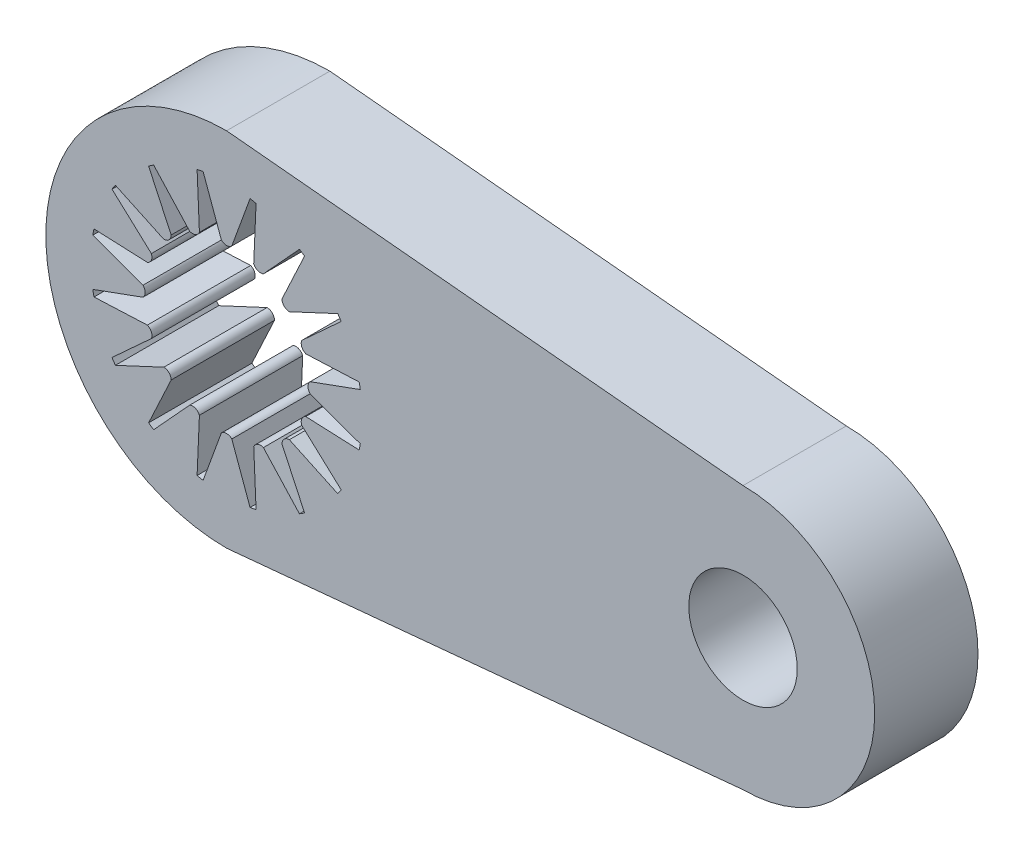
SolidWorks part; units mm, degrees
ref_plane "Ebene vorne" through (0, 0, 0) normal (0, 0, 1) x (1, 0, 0)
ref_plane "Ebene oben" through (0, 0, 0) normal (0, 1, 0) x (1, 0, 0)
ref_plane "Ebene rechts" through (0, 0, 0) normal (1, 0, 0) x (0, 0, -1)
sketch "Sketch1" plane through (0, 0, 0) normal (0, 0, 1) x (1, 0, 0)
  line L32 (12.1788, 4.8622) -> (22.1788, 4.8622) construction
  line L33 (12.1788, 8.3622) -> (22.1788, 7.4122)
  line L34 (12.1788, 1.3622) -> (22.1788, 2.3122)
  line L64 (11.653, 3.3285) -> (11.6192, 2.5524)
  line L65 (11.812, 2.514) -> (12.0777, 3.2441)
  line L66 (12.28, 3.2441) -> (12.5457, 2.514)
  line L67 (12.7385, 2.5524) -> (12.7046, 3.3285)
  line L68 (12.8915, 3.4059) -> (13.4164, 2.8332)
  line L69 (13.5799, 2.9424) -> (13.2515, 3.6465)
  line L70 (13.3946, 3.7895) -> (14.0986, 3.4612)
  line L71 (14.2079, 3.6247) -> (13.6351, 4.1495)
  line L72 (13.7125, 4.3364) -> (14.4886, 4.3025)
  line L73 (14.527, 4.4954) -> (13.797, 4.7611)
  line L74 (13.797, 4.9633) -> (14.527, 5.229)
  line L75 (14.4886, 5.4219) -> (13.7125, 5.388)
  line L76 (13.6351, 5.5749) -> (14.2079, 6.0997)
  line L77 (14.0986, 6.2632) -> (13.3946, 5.9349)
  line L78 (13.2515, 6.0779) -> (13.5799, 6.782)
  line L79 (13.4164, 6.8912) -> (12.8915, 6.3185)
  line L80 (12.7046, 6.3959) -> (12.7385, 7.172)
  line L81 (12.5457, 7.2104) -> (12.28, 6.4803)
  line L82 (12.0777, 6.4803) -> (11.812, 7.2104)
  line L83 (11.6192, 7.172) -> (11.653, 6.3959)
  line L84 (11.4662, 6.3185) -> (10.9413, 6.8912)
  line L85 (10.7778, 6.782) -> (11.1062, 6.0779)
  line L86 (10.9631, 5.9349) -> (10.259, 6.2632)
  line L87 (10.1498, 6.0997) -> (10.7226, 5.5749)
  line L88 (10.6452, 5.388) -> (9.869, 5.4219)
  line L89 (9.8307, 5.229) -> (10.5607, 4.9633)
  line L90 (10.5607, 4.7611) -> (9.8307, 4.4954)
  line L91 (9.869, 4.3025) -> (10.6452, 4.3364)
  line L92 (10.7226, 4.1495) -> (10.1498, 3.6247)
  line L93 (10.259, 3.4612) -> (10.9631, 3.7895)
  line L94 (11.1062, 3.6465) -> (10.7778, 2.9424)
  line L95 (10.9413, 2.8332) -> (11.4662, 3.4059)
  line L96 (10.259, 6.2632) -> (10.0259, 6.3719)
  line L97 (9.9602, 6.2735) -> (10.1498, 6.0997)
  line L98 (9.869, 5.4219) -> (9.6121, 5.4331)
  line L99 (9.589, 5.317) -> (9.8307, 5.229)
  line L100 (9.8307, 4.4954) -> (9.589, 4.4074)
  line L101 (9.6121, 4.2913) -> (9.869, 4.3025)
  line L102 (10.0259, 3.3525) -> (10.259, 3.4612)
  line L103 (10.1498, 3.6247) -> (9.9602, 3.4509)
  line L104 (10.7676, 2.6435) -> (10.9413, 2.8332)
  line L105 (10.7778, 2.9424) -> (10.6691, 2.7093)
  line L106 (11.6192, 2.5524) -> (11.6079, 2.2954)
  line L107 (11.724, 2.2724) -> (11.812, 2.514)
  line L108 (12.5457, 2.514) -> (12.6337, 2.2724)
  line L109 (12.7497, 2.2954) -> (12.7385, 2.5524)
  line L110 (13.6885, 2.7093) -> (13.5799, 2.9424)
  line L111 (13.4164, 2.8332) -> (13.5901, 2.6435)
  line L112 (14.0986, 3.4612) -> (14.3317, 3.3525)
  line L113 (14.3975, 3.4509) -> (14.2079, 3.6247)
  line L114 (14.4886, 4.3025) -> (14.7456, 4.2913)
  line L115 (14.7687, 4.4074) -> (14.527, 4.4954)
  line L116 (14.527, 5.229) -> (14.7687, 5.317)
  line L117 (14.7456, 5.4331) -> (14.4886, 5.4219)
  line L118 (14.3317, 6.3719) -> (14.0986, 6.2632)
  line L119 (14.2079, 6.0997) -> (14.3975, 6.2735)
  line L120 (13.5799, 6.782) -> (13.6885, 7.0151)
  line L121 (13.5901, 7.0809) -> (13.4164, 6.8912)
  line L122 (12.7385, 7.172) -> (12.7497, 7.429)
  line L123 (12.6337, 7.452) -> (12.5457, 7.2104)
  line L124 (11.6079, 7.429) -> (11.6192, 7.172)
  line L125 (11.812, 7.2104) -> (11.724, 7.452)
  line L126 (10.6691, 7.0151) -> (10.7778, 6.782)
  line L127 (10.9413, 6.8912) -> (10.7676, 7.0809)
  arc A2 (12.8379, 8.2996) -> (12.8379, 1.4248) centre (12.1788, 4.8622) ccw
  circle A4 centre (22.1788, 4.8622) radius 1.05
  arc A6 (22.1788, 2.3122) -> (22.1788, 7.4122) centre (22.1788, 4.8622) ccw
  arc A64 (11.653, 3.3285) -> (11.4662, 3.4059) centre (11.5209, 3.2738) ccw
  arc A66 (12.28, 3.2441) -> (12.0777, 3.2441) centre (12.1788, 3.1429) ccw
  arc A68 (12.8915, 3.4059) -> (12.7046, 3.3285) centre (12.8368, 3.2738) ccw
  arc A70 (13.3946, 3.7895) -> (13.2515, 3.6465) centre (13.3946, 3.6465) ccw
  arc A72 (13.7125, 4.3364) -> (13.6351, 4.1495) centre (13.7672, 4.2043) ccw
  arc A74 (13.797, 4.9633) -> (13.797, 4.7611) centre (13.8981, 4.8622) ccw
  arc A76 (13.6351, 5.5749) -> (13.7125, 5.388) centre (13.7672, 5.5201) ccw
  arc A78 (13.2515, 6.0779) -> (13.3946, 5.9349) centre (13.3946, 6.0779) ccw
  arc A80 (12.7046, 6.3959) -> (12.8915, 6.3185) centre (12.8368, 6.4506) ccw
  arc A82 (12.0777, 6.4803) -> (12.28, 6.4803) centre (12.1788, 6.5815) ccw
  arc A84 (11.4662, 6.3185) -> (11.653, 6.3959) centre (11.5209, 6.4506) ccw
  arc A86 (10.9631, 5.9349) -> (11.1062, 6.0779) centre (10.9631, 6.0779) ccw
  arc A88 (10.6452, 5.388) -> (10.7226, 5.5749) centre (10.5904, 5.5201) ccw
  arc A90 (10.5607, 4.7611) -> (10.5607, 4.9633) centre (10.4596, 4.8622) ccw
  arc A92 (10.7226, 4.1495) -> (10.6452, 4.3364) centre (10.5904, 4.2043) ccw
  arc A94 (11.1062, 3.6465) -> (10.9631, 3.7895) centre (10.9631, 3.6465) ccw
  arc A97 (10.0259, 6.3719) -> (9.9602, 6.2735) centre (12.1788, 4.8622) ccw
  arc A99 (9.6121, 5.4331) -> (9.589, 5.317) centre (12.1788, 4.8622) ccw
  arc A101 (9.589, 4.4074) -> (9.6121, 4.2913) centre (12.1788, 4.8622) ccw
  arc A103 (9.9602, 3.4509) -> (10.0259, 3.3525) centre (12.1788, 4.8622) ccw
  arc A105 (10.6691, 2.7093) -> (10.7676, 2.6435) centre (12.1788, 4.8622) ccw
  arc A107 (11.6079, 2.2954) -> (11.724, 2.2724) centre (12.1788, 4.8622) ccw
  arc A109 (12.6337, 2.2724) -> (12.7497, 2.2954) centre (12.1788, 4.8622) ccw
  arc A111 (13.5901, 2.6435) -> (13.6885, 2.7093) centre (12.1788, 4.8622) ccw
  arc A113 (14.3317, 3.3525) -> (14.3975, 3.4509) centre (12.1788, 4.8622) ccw
  arc A115 (14.7456, 4.2913) -> (14.7687, 4.4074) centre (12.1788, 4.8622) ccw
  arc A117 (14.7687, 5.317) -> (14.7456, 5.4331) centre (12.1788, 4.8622) ccw
  arc A119 (14.3975, 6.2735) -> (14.3317, 6.3719) centre (12.1788, 4.8622) ccw
  arc A121 (13.6885, 7.0151) -> (13.5901, 7.0809) centre (12.1788, 4.8622) ccw
  arc A123 (12.7497, 7.429) -> (12.6337, 7.452) centre (12.1788, 4.8622) ccw
  arc A125 (11.724, 7.452) -> (11.6079, 7.429) centre (12.1788, 4.8622) ccw
  arc A127 (10.7676, 7.0809) -> (10.6691, 7.0151) centre (12.1788, 4.8622) ccw
  dimension "D1" = 2.1
  dimension "D2" = 5.1
  dimension "D3" = 7
  dimension "D4" = 10
extrude "Boss-Extrude3" add sketch "Sketch1" along normal blind 2
